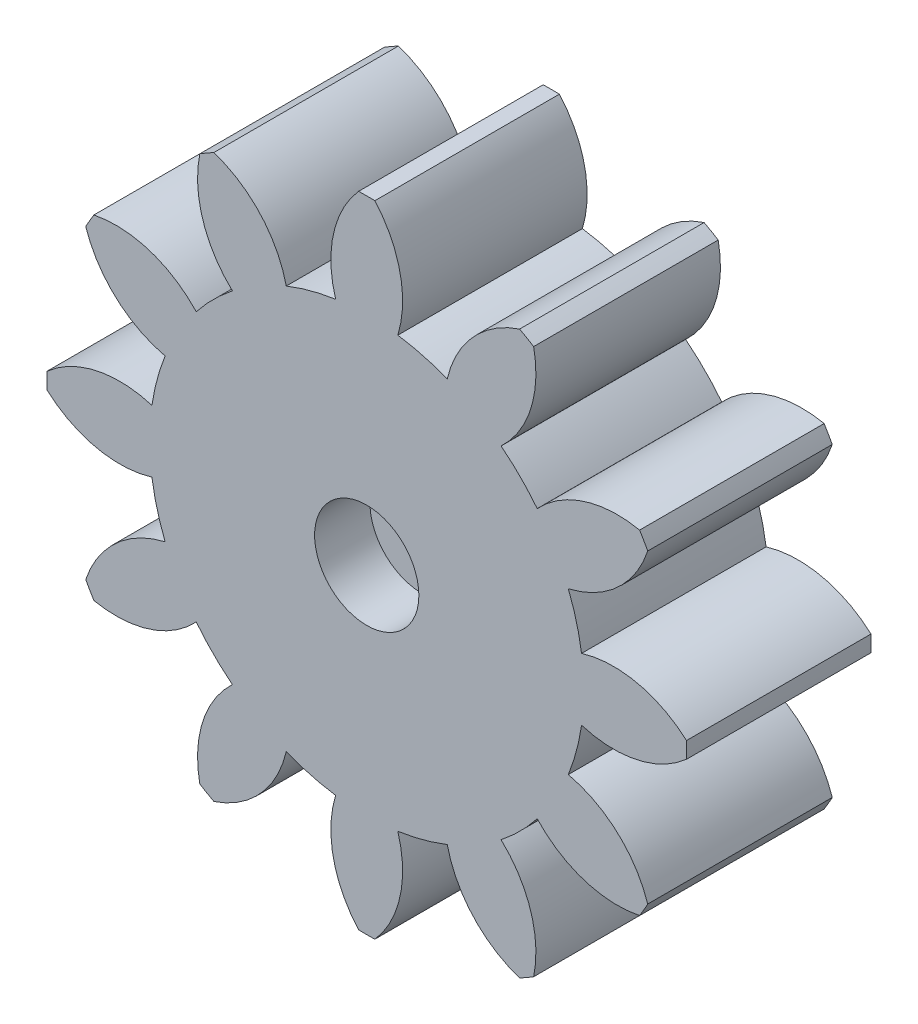
SolidWorks part; units mm, degrees
ref_plane "Front Plane" through (0, 0, 0) normal (0, 0, 1) x (1, 0, 0)
ref_plane "Top Plane" through (0, 0, 0) normal (0, 1, 0) x (1, 0, 0)
ref_plane "Right Plane" through (0, 0, 0) normal (1, 0, 0) x (0, 0, -1)
sketch "Sketch1" plane through (0, 0, 0) normal (0, 0, 1) x (1, 0, 0)
  arc A96 (10.9244, -4.3614) -> (11.6416, -1.6851) centre (0, 0) ccw
  arc A97 (11.6416, -1.6851) -> (17.3299, -0.4402) centre (13.3779, 3.9992) ccw
  arc A98 (17.3299, -0.4402) -> (17.3299, 0.4402) centre (0, 0) ccw
  arc A99 (17.3299, 0.4402) -> (11.6416, 1.6851) centre (13.3779, -3.9992) ccw
  arc A100 (11.6416, 1.6851) -> (10.9244, 4.3614) centre (0, 0) ccw
  arc A101 (10.9244, 4.3614) -> (15.2282, 8.2838) centre (9.586, 10.1524) ccw
  arc A102 (15.2282, 8.2838) -> (14.7881, 9.0462) centre (0, 0) ccw
  arc A103 (14.7881, 9.0462) -> (9.2393, 7.2801) centre (13.5852, 3.2255) ccw
  arc A104 (9.2393, 7.2801) -> (7.2801, 9.2393) centre (0, 0) ccw
  arc A105 (7.2801, 9.2393) -> (9.0462, 14.7881) centre (3.2255, 13.5852) ccw
  arc A106 (9.0462, 14.7881) -> (8.2838, 15.2282) centre (0, 0) ccw
  arc A107 (8.2838, 15.2282) -> (4.3614, 10.9244) centre (10.1524, 9.586) ccw
  arc A108 (4.3614, 10.9244) -> (1.6851, 11.6416) centre (0, 0) ccw
  arc A109 (1.6851, 11.6416) -> (0.4402, 17.3299) centre (-3.9992, 13.3779) ccw
  arc A110 (0.4402, 17.3299) -> (-0.4402, 17.3299) centre (0, 0) ccw
  arc A111 (-0.4402, 17.3299) -> (-1.6851, 11.6416) centre (3.9992, 13.3779) ccw
  arc A112 (-1.6851, 11.6416) -> (-4.3614, 10.9244) centre (0, 0) ccw
  arc A113 (-4.3614, 10.9244) -> (-8.2838, 15.2282) centre (-10.1524, 9.586) ccw
  arc A114 (-8.2838, 15.2282) -> (-9.0462, 14.7881) centre (0, 0) ccw
  arc A115 (-9.0462, 14.7881) -> (-7.2801, 9.2393) centre (-3.2255, 13.5852) ccw
  arc A116 (-7.2801, 9.2393) -> (-9.2393, 7.2801) centre (0, 0) ccw
  arc A117 (-9.2393, 7.2801) -> (-14.7881, 9.0462) centre (-13.5852, 3.2255) ccw
  arc A118 (-14.7881, 9.0462) -> (-15.2282, 8.2838) centre (0, 0) ccw
  arc A119 (-15.2282, 8.2838) -> (-10.9244, 4.3614) centre (-9.586, 10.1524) ccw
  arc A120 (-10.9244, 4.3614) -> (-11.6416, 1.6851) centre (0, 0) ccw
  arc A121 (-11.6416, 1.6851) -> (-17.3299, 0.4402) centre (-13.3779, -3.9992) ccw
  arc A122 (-17.3299, 0.4402) -> (-17.3299, -0.4402) centre (0, 0) ccw
  arc A123 (-17.3299, -0.4402) -> (-11.6416, -1.6851) centre (-13.3779, 3.9992) ccw
  arc A124 (-11.6416, -1.6851) -> (-10.9244, -4.3614) centre (0, 0) ccw
  arc A125 (-10.9244, -4.3614) -> (-15.2282, -8.2838) centre (-9.586, -10.1524) ccw
  arc A126 (-15.2282, -8.2838) -> (-14.7881, -9.0462) centre (0, 0) ccw
  arc A127 (-14.7881, -9.0462) -> (-9.2393, -7.2801) centre (-13.5852, -3.2255) ccw
  arc A128 (-9.2393, -7.2801) -> (-7.2801, -9.2393) centre (0, 0) ccw
  arc A129 (-7.2801, -9.2393) -> (-9.0462, -14.7881) centre (-3.2255, -13.5852) ccw
  arc A130 (-9.0462, -14.7881) -> (-8.2838, -15.2282) centre (0, 0) ccw
  arc A131 (-8.2838, -15.2282) -> (-4.3614, -10.9244) centre (-10.1524, -9.586) ccw
  arc A132 (-4.3614, -10.9244) -> (-1.6851, -11.6416) centre (0, 0) ccw
  arc A133 (-1.6851, -11.6416) -> (-0.4402, -17.3299) centre (3.9992, -13.3779) ccw
  arc A134 (-0.4402, -17.3299) -> (0.4402, -17.3299) centre (0, 0) ccw
  arc A135 (0.4402, -17.3299) -> (1.6851, -11.6416) centre (-3.9992, -13.3779) ccw
  arc A136 (1.6851, -11.6416) -> (4.3614, -10.9244) centre (0, 0) ccw
  arc A137 (4.3614, -10.9244) -> (8.2838, -15.2282) centre (10.1524, -9.586) ccw
  arc A138 (8.2838, -15.2282) -> (9.0462, -14.7881) centre (0, 0) ccw
  arc A139 (9.0462, -14.7881) -> (7.2801, -9.2393) centre (3.2255, -13.5852) ccw
  arc A140 (7.2801, -9.2393) -> (9.2393, -7.2801) centre (0, 0) ccw
  arc A141 (9.2393, -7.2801) -> (14.7881, -9.0462) centre (13.5852, -3.2255) ccw
  arc A142 (14.7881, -9.0462) -> (15.2282, -8.2838) centre (0, 0) ccw
  arc A143 (15.2282, -8.2838) -> (10.9244, -4.3614) centre (9.586, -10.1524) ccw
extrude "Boss-Extrude1" add sketch "Sketch1" along normal blind 10
sketch "Sketch3" plane through (0, 0, 10) normal (0, 0, 1) x (1, 0, 0)
  circle A0 centre (0, 0) radius 2.825
  dimension "D1" = 5.65
extrude "Cut-Extrude1" cut sketch "Sketch3" against normal blind 3
sketch "Sketch4" plane through (0, 0, 0) normal (0, 0, -1) x (-1, 0, 0)
  circle A0 centre (0, 0) radius 2.825 construction
  circle A1 centre (0, 0) radius 2.825
extrude "Cut-Extrude2" cut sketch "Sketch4" against normal offset from surface (5 mm away) 2 up to face at (2.825, 0, 7)
sketch "Sketch5" plane through (0, 0, 5) normal (0, 0, -1) x (-1, 0, 0)
  circle A0 centre (0, 0) radius 1.375
  dimension "D1" = 2.75
extrude "Cut-Extrude3" cut sketch "Sketch5" against normal up to next
sketch "Sketch6" plane through (0, 0, 0) normal (0, 0, -1) x (-1, 0, 0)
  text T0 "<i>.65</i>" font "Century Gothic" height in points 22
extrude "Cut-Extrude4" cut sketch "Sketch6" against normal blind 0.4
sketch "Sketch7" plane through (0, 0, 10) normal (0, 0, 1) x (1, 0, 0)
  point P0 (0, 0)
sketch "Sketch8" plane through (0, 0, 10) normal (0, 0, 1) x (1, 0, 0)
  line L0 (0, 0) -> (0, -17.3355) construction
  arc A0 (-0.4402, -17.3299) -> (0.4402, -17.3299) centre (0, 0) ccw construction
